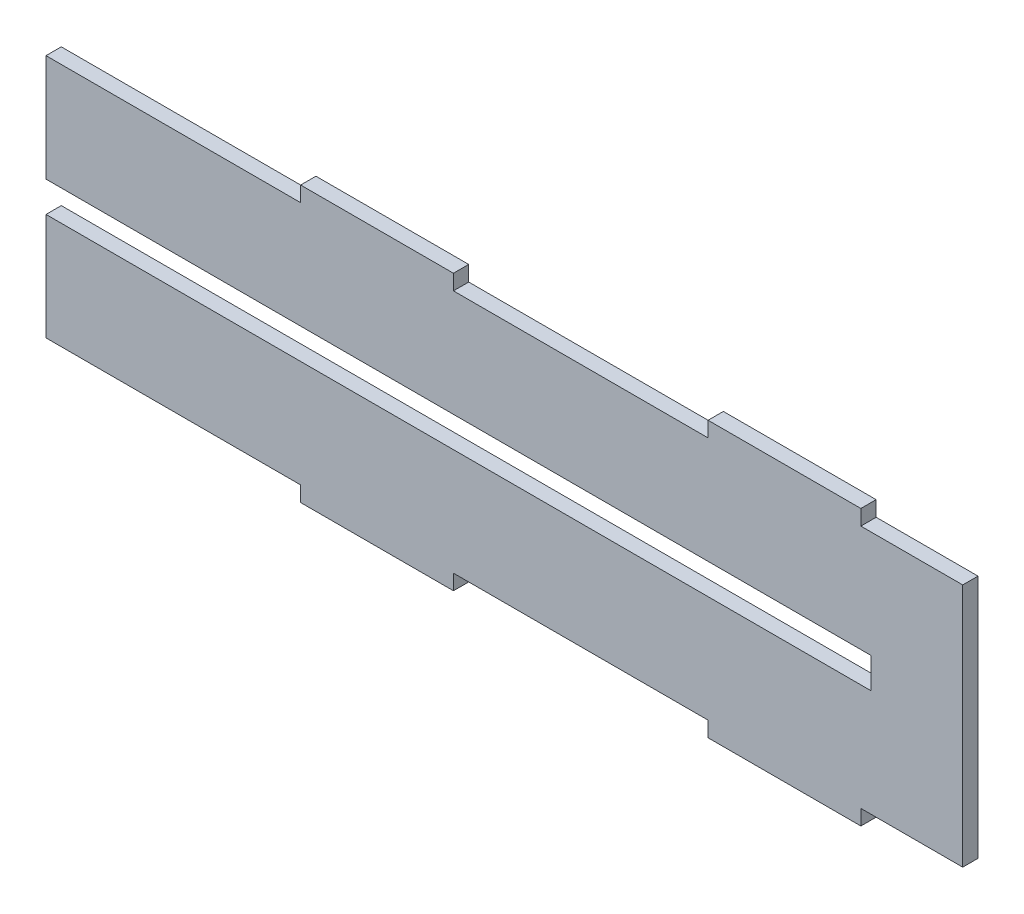
SolidWorks part; units mm, degrees
material "ACM"
ref_plane "Plano frontal" through (0, 0, 0) normal (0, 0, 1) x (1, 0, 0)
ref_plane "Plano superior" through (0, 0, 0) normal (0, 1, 0) x (1, 0, 0)
ref_plane "Plano direito" through (0, 0, 0) normal (1, 0, 0) x (0, 0, -1)
sketch "Esboço1" plane through (0, 0, 0) normal (0, 0, 1) x (1, 0, 0)
  line L0 (0, -48) -> (50, -48)
  line L1 (0, 0) -> (50, 0)
  line L2 (0, 0) -> (0, -48)
  line L3 (50, -51) -> (80, -51)
  line L5 (50, -48) -> (50, -51)
  line L6 (80, -51) -> (80, -48)
  line L7 (80, -48) -> (130, -48)
  line L8 (130, -48) -> (130, -51)
  line L9 (160, -51) -> (160, -48)
  line L10 (160, -48) -> (180, -48)
  line L11 (130, -51) -> (160, -51)
  line L12 (0, -24) -> (180, -24) construction
  line L13 (0, 0) -> (50, 0)
  line L14 (80, 0) -> (130, 0)
  line L15 (160, 0) -> (180, 0)
  line L16 (160, 3) -> (160, 0)
  line L17 (130, 3) -> (160, 3)
  line L18 (130, 0) -> (130, 3)
  line L19 (80, 3) -> (80, 0)
  line L20 (50, 3) -> (80, 3)
  line L21 (50, 0) -> (50, 3)
  line L22 (80, 0) -> (130, 0)
  line L23 (160, 0) -> (180, 0)
  line L24 (180, 0) -> (180, -48)
  line L25 (0, -21) -> (162, -21)
  line L26 (0, -21) -> (0, -27)
  line L27 (0, -27) -> (162, -27)
  line L28 (162, -21) -> (162, -27)
  point P27 (0, -24)
  dimension "D2" = 48
  dimension "D3" = 50
  dimension "D4" = 3
  dimension "D5" = 30
  dimension "D6" = 50
  dimension "D7" = 3
  dimension "D8" = 30
  dimension "D9" = 3
  dimension "D10" = 180
  dimension "D11" = 162
  dimension "D12" = 6
  dimension "D14" = 30
extrude "Ressalto-extrusão1" add sketch "Esboço1" along normal blind 3
